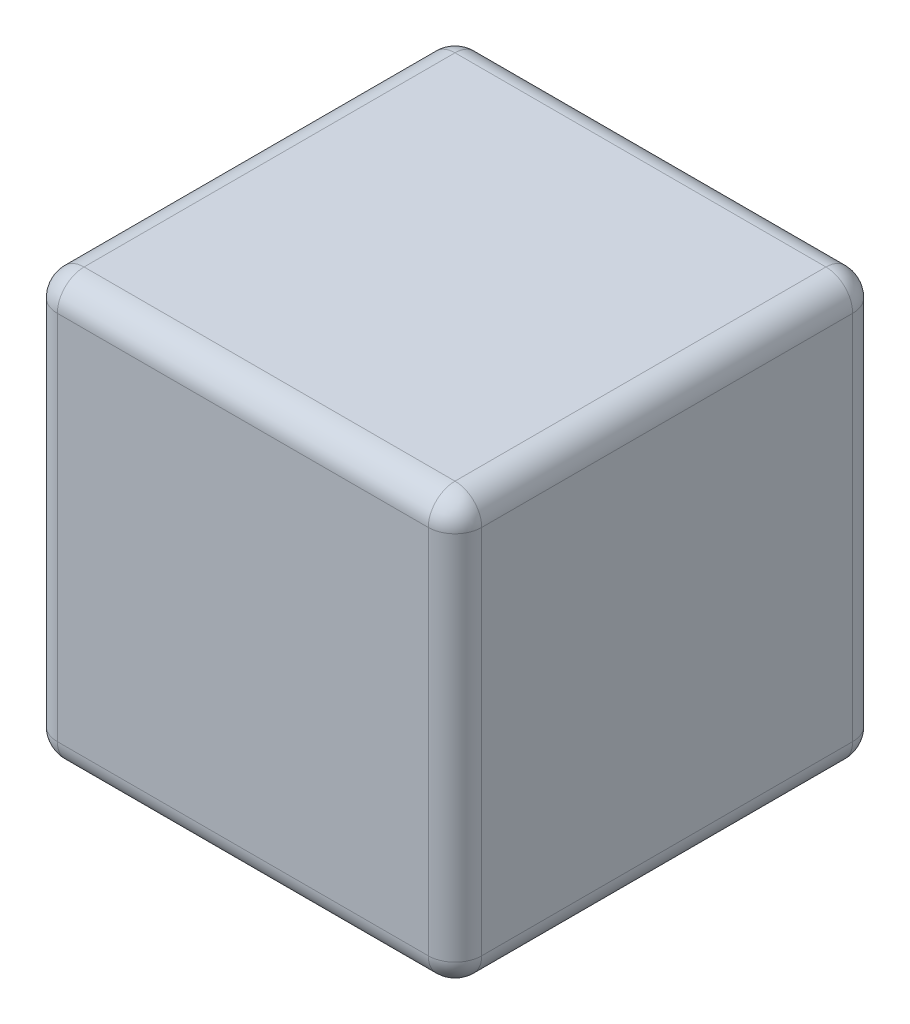
SolidWorks part; units mm, degrees
ref_plane "Front Plane" through (0, 0, 0) normal (0, 0, 1) x (1, 0, 0)
ref_plane "Top Plane" through (0, 0, 0) normal (0, 1, 0) x (1, 0, 0)
ref_plane "Right Plane" through (0, 0, 0) normal (1, 0, 0) x (0, 0, -1)
sketch "Sketch1" plane through (0, 0, 0) normal (0, 0, 1) x (1, 0, 0)
  line L1 (-0.7938, -0.7938) -> (0.7937, -0.7938)
  line L2 (-0.7938, -0.7938) -> (-0.7938, 0.7937)
  line L3 (-0.7938, 0.7937) -> (0.7937, 0.7937)
  line L4 (0.7937, -0.7938) -> (0.7937, 0.7937)
  line L5 (-0.7938, -0.7938) -> (0.7937, 0.7937) construction
  line L6 (-0.7938, 0.7937) -> (0.7937, -0.7938) construction
  point P0 (0, 0)
  dimension "D1" = 1.5875
  dimension "D2" = 1.5875
extrude "Boss-Extrude1" add sketch "Sketch1" along normal blind 1.5875
fillet "Fillet1" radius 0.1 12 edges at (-0.7938, -0.7938, 0.7937) (0, -0.7938, 0) (0.7937, -0.7938, 0.7937) (0.7937, 0, 0) (0, -0.7938, 1.5875) (-0.7938, 0, 1.5875) (0.7937, 0, 1.5875) (0.7937, 0.7937, 0.7937) (0, 0.7937, 1.5875) (-0.7938, 0.7937, 0.7937) (0, 0.7937, 0) (-0.7938, 0, 0)
